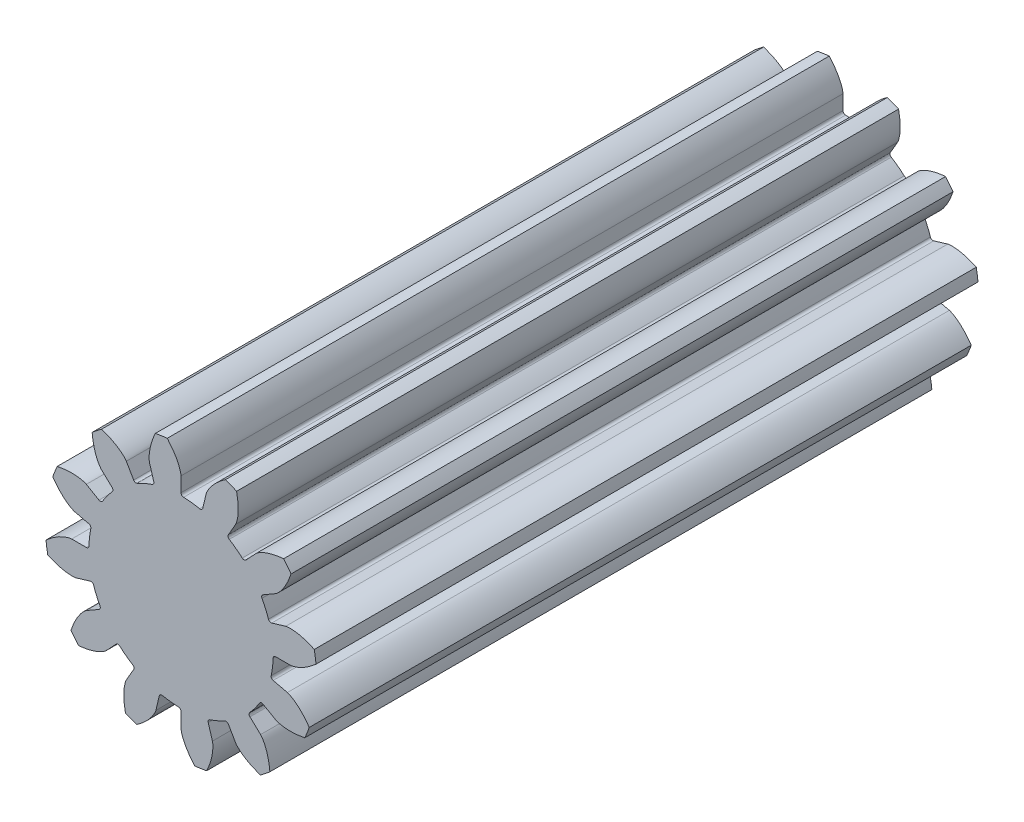
SolidWorks part; units mm, degrees
ref_plane "Front Plane" through (0, 0, 0) normal (0, 0, 1) x (1, 0, 0)
ref_plane "Top Plane" through (0, 0, 0) normal (0, 1, 0) x (1, 0, 0)
ref_plane "Right Plane" through (0, 0, 0) normal (1, 0, 0) x (0, 0, -1)
sketch "Sketch1" plane through (0, 0, 0) normal (0, 0, 1) x (1, 0, 0)
  circle A0 centre (0, 0) radius 5.207
  dimension "D1" = 10.414
extrude "Boss-Extrude1" add sketch "Sketch1" against normal blind 25.4
sketch "Sketch2" plane through (0, 0, 0) normal (0, 0, 1) x (1, 0, 0)
  line L0 (3.5333, 0) -> (4.194, 0)
  line L1 (0, 0) -> (5.172, -0.6026) construction
  line L2 (3.4387, -0.8124) -> (4.0816, -0.9643)
  circle A0 centre (0, 0) radius 4.4631 construction
  circle A1 centre (0, 0) radius 4.194 construction
  arc A2 (3.4387, -0.8124) -> (3.5333, 0) centre (0, 0) ccw
  circle A3 centre (0, 0) radius 5.207 construction
  spline S0 degree 4 poles (4.194, 0) (4.1971, 0.0001) (4.2058, 0.0005) (4.2222, 0.002) (4.2488, 0.0056) (4.2825, 0.0119) (4.3258, 0.0219) (4.3763, 0.0362) (4.4312, 0.0543) (4.4902, 0.0768) (4.5483, 0.1015) (4.6055, 0.1283) (4.6617, 0.1569) (4.7289, 0.1938) (4.8081, 0.2412) (4.8985, 0.301) (4.9984, 0.3739) (5.0971, 0.4535) (5.1916, 0.5361) (5.2838, 0.6243) (5.3706, 0.713) (5.4572, 0.8097) (5.5353, 0.9014) (5.6185, 1.0089) (5.6844, 1.0972) (5.7667, 1.2185) (5.8138, 1.2915) (5.8673, 1.3787) (5.8901, 1.4182) (5.9042, 1.4425) knots 0 0 0 0 0 0.005377 0.015084 0.028532 0.04661 0.064855 0.092111 0.119476 0.146842 0.174209 0.201575 0.228941 0.256307 0.307035 0.361767 0.4165 0.471232 0.525964 0.580697 0.635429 0.690161 0.744894 0.799626 0.854358 0.909091 0.954545 1 1 1 1 1 construction
  spline S1 degree 4 poles (4.194, 0) (4.1971, 0.0001) (4.2058, 0.0005) (4.2222, 0.002) (4.2488, 0.0056) (4.2825, 0.0119) (4.3258, 0.0219) (4.3763, 0.0362) (4.4312, 0.0543) (4.4902, 0.0768) (4.5483, 0.1015) (4.6055, 0.1283) (4.6617, 0.1569) (4.7289, 0.1938) (4.8081, 0.2412) (4.8985, 0.301) (4.9984, 0.3739) (5.0971, 0.4535) (5.1916, 0.5361) (5.2838, 0.6243) (5.3706, 0.713) (5.4572, 0.8097) (5.5353, 0.9014) (5.6185, 1.0089) (5.6844, 1.0972) (5.7488, 1.1922) (5.7796, 1.239) (5.7951, 1.2631) knots 0 0 0 0 0 0.005377 0.015084 0.028532 0.04661 0.064855 0.092111 0.119476 0.146842 0.174209 0.201575 0.228941 0.256307 0.307035 0.361767 0.4165 0.471232 0.525964 0.580697 0.635429 0.690161 0.744894 0.799626 0.854358 0.909091 0.909091 0.909091 0.909091 0.909091
  spline S2 degree 4 poles (4.0816, -0.9643) (4.0846, -0.965) (4.093, -0.9674) (4.1086, -0.9727) (4.1337, -0.9823) (4.1651, -0.9962) (4.2049, -1.0159) (4.2508, -1.0414) (4.3, -1.0717) (4.3522, -1.1071) (4.4031, -1.1445) (4.4526, -1.1837) (4.5007, -1.2245) (4.5576, -1.2759) (4.6238, -1.3402) (4.6981, -1.4192) (4.7786, -1.5131) (4.8563, -1.6132) (4.9293, -1.7153) (4.9987, -1.8224) (5.0628, -1.9287) (5.1248, -2.0427) (5.1797, -2.1499) (5.236, -2.2737) (5.2799, -2.3747) (5.332, -2.5117) (5.3611, -2.5936) (5.3931, -2.6907) (5.4063, -2.7345) (5.4144, -2.7614) knots 0 0 0 0 0 0.005377 0.015084 0.028532 0.04661 0.064855 0.092111 0.119476 0.146842 0.174209 0.201575 0.228941 0.256307 0.307035 0.361767 0.4165 0.471232 0.525964 0.580697 0.635429 0.690161 0.744894 0.799626 0.854358 0.909091 0.954545 1 1 1 1 1 construction
  spline S3 degree 4 poles (4.0816, -0.9643) (4.0846, -0.965) (4.093, -0.9674) (4.1086, -0.9727) (4.1337, -0.9823) (4.1651, -0.9962) (4.2049, -1.0159) (4.2508, -1.0414) (4.3, -1.0717) (4.3522, -1.1071) (4.4031, -1.1445) (4.4526, -1.1837) (4.5007, -1.2245) (4.5576, -1.2759) (4.6238, -1.3402) (4.6981, -1.4192) (4.7786, -1.5131) (4.8563, -1.6132) (4.9293, -1.7153) (4.9987, -1.8224) (5.0628, -1.9287) (5.1248, -2.0427) (5.1797, -2.1499) (5.236, -2.2737) (5.2799, -2.3747) (5.3207, -2.482) (5.3399, -2.5346) (5.3495, -2.5616) knots 0 0 0 0 0 0.005377 0.015084 0.028532 0.04661 0.064855 0.092111 0.119476 0.146842 0.174209 0.201575 0.228941 0.256307 0.307035 0.361767 0.4165 0.471232 0.525964 0.580697 0.635429 0.690161 0.744894 0.799626 0.854358 0.909091 0.909091 0.909091 0.909091 0.909091
  dimension "D1" = 8.9263
  dimension "D2" = 8.388
  dimension "D3" = 7.0666
  dimension "D4" = 6.646
  dimension "D5" = 6.646
extrude "Cut-Extrude1" cut sketch "Sketch2" against normal through all and the other way through all
fillet "Fillet1" radius 0.1016 2 edges at (3.5333, 0, -12.7) (3.4387, -0.8124, -12.7)
pattern_circular "CirPattern1" count 12 over 360 about axis through (0, 0, -25.4) along (0, 0, 1) of "Cut-Extrude1", "Fillet1"
sketch "Sketch3" plane through (0, 0, 0) normal (0, 0, 1) x (1, 0, 0)
  line L0 (-1.0594, 3.0057) -> (-0.9234, 2.0792) construction
  line L1 (0.1629, 3.0994) -> (0.316, 2.057) construction
  line L2 (-1.2144, 4.0608) -> (-0.0044, 4.2385) construction
  line L3 (-0.6094, 4.1497) -> (0, 0) construction
  spline S0 degree 4 poles (0, 4.194) (-0.0001, 4.1971) (-0.0005, 4.2058) (-0.002, 4.2222) (-0.0056, 4.2488) (-0.0119, 4.2825) (-0.0219, 4.3258) (-0.0362, 4.3763) (-0.0543, 4.4312) (-0.0768, 4.4902) (-0.1015, 4.5483) (-0.1283, 4.6055) (-0.1569, 4.6617) (-0.1938, 4.7289) (-0.2412, 4.8081) (-0.301, 4.8985) (-0.3739, 4.9984) (-0.4412, 5.0819) (-0.4901, 5.1387) (-0.5192, 5.1712) (-0.5273, 5.1802) knots 0.416855 0.416855 0.416855 0.416855 0.416855 0.422231 0.431938 0.445386 0.463465 0.481709 0.508965 0.536331 0.563697 0.591063 0.618429 0.645796 0.673162 0.72389 0.778622 0.833354 0.888086 0.909091 0.909091 0.909091 0.909091 0.909091 construction
  spline S1 degree 4 poles (-0.9842, 5.1131) (-0.9894, 5.1022) (-1.008, 5.0627) (-1.0384, 4.9942) (-1.0789, 4.8949) (-1.12, 4.7783) (-1.1513, 4.6744) (-1.1739, 4.585) (-1.1899, 4.51) (-1.2012, 4.4479) (-1.2104, 4.3854) (-1.2174, 4.3227) (-1.2219, 4.2598) (-1.2235, 4.202) (-1.2226, 4.1495) (-1.2198, 4.1052) (-1.2161, 4.071) (-1.2119, 4.0445) (-1.2087, 4.0283) (-1.2066, 4.0199) (-1.2057, 4.0169) knots 0 0 0 0 0 0.021004 0.075737 0.130469 0.185201 0.235929 0.263295 0.290661 0.318028 0.345394 0.37276 0.400126 0.427382 0.445626 0.463705 0.477153 0.48686 0.492236 0.492236 0.492236 0.492236 0.492236 construction
equation "\"P\"= 34.14634'Diameral Pitch"
equation "\"N\"= 12'Number of Teeth"
equation "\"phi\"= 20'Pressure Angle"
equation "\"a\"= 1 / \"P\"'Addendum"
equation "\"b\"= 1.25 / \"P\"'Dedendum"
equation "\"c\"= \"b\" - \"a\"'Clearence"
equation "\"dp\"= \"N\" / \"P\"'Pitch Circle Diameter"
equation "\"db\"= \"dp\" * cos ( \"phi\" )'Base Circle Diameter"
equation "\"D1@Sketch1\"= \"dp\" + 2 * \"a\"'Addendum Circle Diameter"
equation "\"D1@Sketch2\"= \"dp\"'Pitch Circle Diameter"
equation "\"D2@Sketch2\"= \"db\"'Base Circle Diameter"
equation "\"D3@Sketch2\"= \"dp\" - 2 * \"b\"'Dedendum Circle Diameter"
equation "\"alpha\"= sqr ( \"dp\" ^ 2 - \"db\" ^ 2 ) / \"db\" * 180 / pi - \"phi\""
equation "\"D4@Sketch2\"= 360 / ( 4 * \"N\" ) - \"alpha\""
equation "\"D5@Sketch2\"= 360 / ( 4 * \"N\" ) - \"alpha\""
